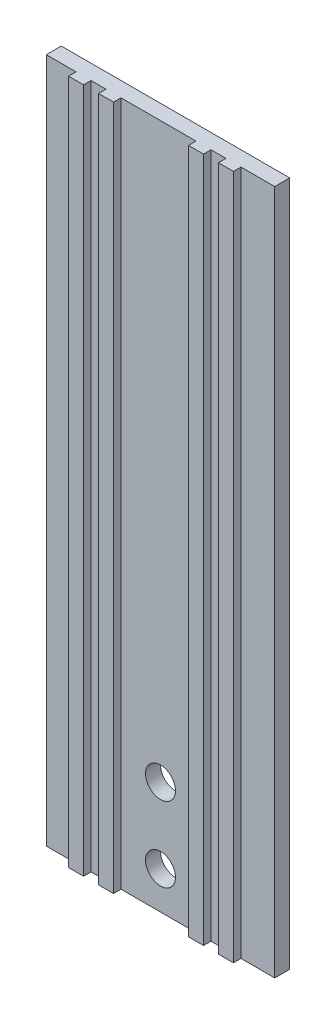
SolidWorks part; units mm, degrees
ref_plane "Front Plane" through (0, 0, 0) normal (0, 0, 1) x (1, 0, 0)
ref_plane "Top Plane" through (0, 0, 0) normal (0, 1, 0) x (1, 0, 0)
ref_plane "Right Plane" through (0, 0, 0) normal (1, 0, 0) x (0, 0, -1)
sketch "Sketch1" plane through (0, 0, 0) normal (0, 0, 1) x (1, 0, 0)
  line L1 (-76.2, 228.6) -> (76.2, 228.6)
  line L2 (76.2, 228.6) -> (76.2, -228.6)
  line L3 (76.2, -228.6) -> (-76.2, -228.6)
  line L4 (-76.2, -228.6) -> (-76.2, 228.6)
  circle A0 centre (0, -203.6) radius 10
  circle A1 centre (0, -153.6) radius 10
  point P4 (0, 0)
  point P8 (0, 228.6)
  dimension "D1" = 20
  dimension "D3" = 25
  dimension "D4" = 20
  dimension "D2" = 50
extrude "Boss-Extrude1" add sketch "Sketch1" along normal blind 10
sketch "Sketch2" plane through (0, 0, 10) normal (0, 0, 1) x (1, 0, 0)
  line L0 (33.6658, 228.6) -> (33.6658, -228.6)
  line L1 (-76.2, 228.6) -> (76.2, 228.6) construction
  line L2 (76.2, -228.6) -> (-76.2, -228.6) construction
  line L3 (53.6658, 228.6) -> (53.6658, -228.6)
  line L4 (-26.3342, 228.6) -> (-26.3342, -228.6)
  line L5 (-46.3342, 228.6) -> (-46.3342, -228.6)
  dimension "D1" = 20
  dimension "D2" = 20
  dimension "D3" = 60
extrude "Extrude-Thin1" add sketch "Sketch2" along normal blind 5 thin
sketch "Sketch3" plane through (0, 0, 0) normal (0, 0, 1) x (1, 0, 0)
  line L0 (-76.2, 228.6) -> (-76.2, 248.6)
  line L1 (-76.2, 248.6) -> (76.2, 248.6)
  line L2 (76.2, 248.6) -> (76.2, 228.6)
  dimension "D1" = 20
ref_plane "Plane1" through (0, 0, -152.4) normal (0, 0, -1) x (-1, 0, 0)
sketch "Sketch4" plane through (0, 0, 10) normal (0, 0, 1) x (1, 0, 0)
  line L2 (33.6658, 218.6) -> (33.6658, -218.6)
  line L4 (43.6658, 218.6) -> (43.6658, -218.6)
  arc A0 (43.6658, 218.6) -> (33.6658, 218.6) centre (38.6658, 218.6) ccw
  arc A1 (33.6658, -218.6) -> (43.6658, -218.6) centre (38.6658, -218.6) ccw
sketch "Sketch6" plane through (0, 0, 10) normal (0, 0, 1) x (1, 0, 0)
  line L0 (-46.3342, 218.6) -> (-46.3342, -218.6)
  line L1 (-36.3342, 218.6) -> (-36.3342, -218.6)
  line L2 (-41.3342, 218.6) -> (-41.3342, -218.6) construction
  line L3 (-36.3342, -218.6) -> (33.6658, -218.6) construction
  line L4 (33.6658, 218.6) -> (-36.3342, 218.6) construction
  line L5 (-36.3342, 228.6) -> (-36.3342, 218.6) construction
  line L6 (-46.3342, 228.6) -> (-46.3342, 218.6) construction
  arc A0 (-36.3342, 218.6) -> (-46.3342, 218.6) centre (-41.3342, 218.6) ccw
  arc A1 (-46.3342, -218.6) -> (-36.3342, -218.6) centre (-41.3342, -218.6) ccw
